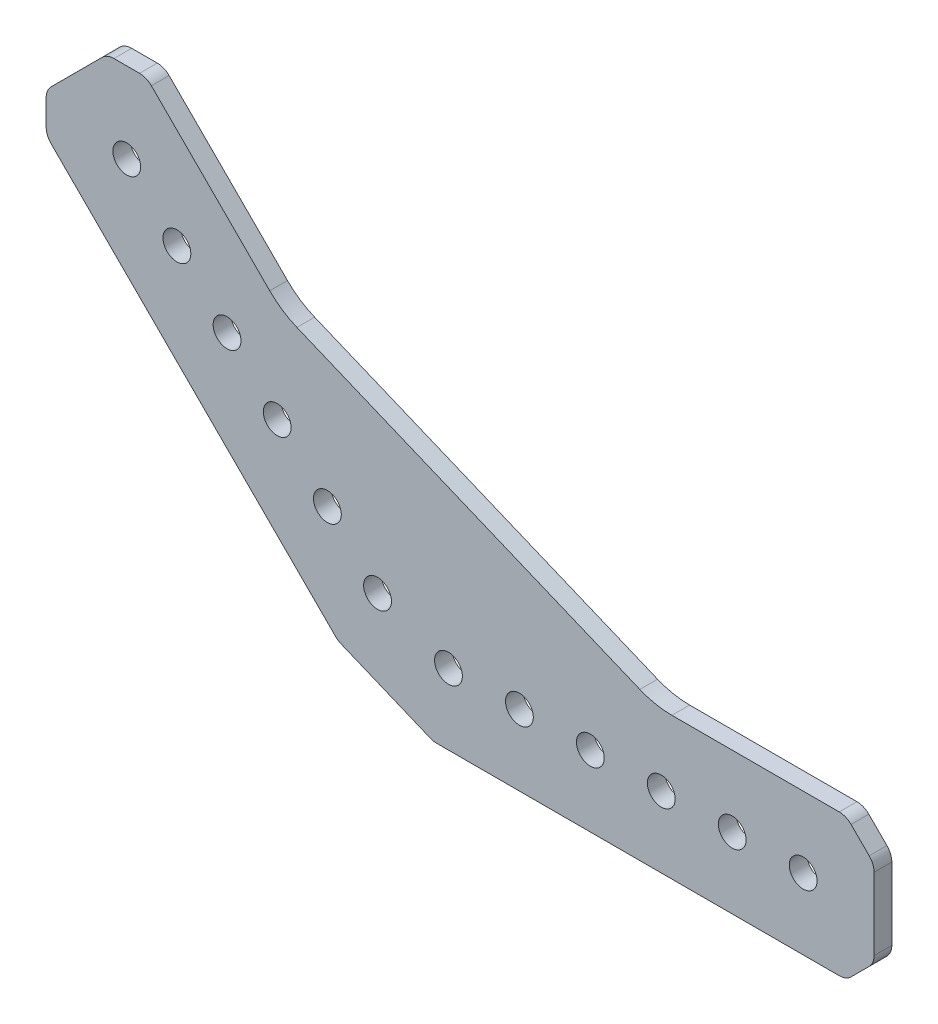
SolidWorks part; units mm, degrees
material "5052-H32"
ref_plane "Front Plane" through (0, 0, 0) normal (0, 0, 1) x (1, 0, 0)
ref_plane "Top Plane" through (0, 0, 0) normal (0, 1, 0) x (1, 0, 0)
ref_plane "Right Plane" through (0, 0, 0) normal (1, 0, 0) x (0, 0, -1)
ref_plane "Plane1" through (0, 0, 3.175) normal (0, 0, 1) x (1, 0, 0)
sketch "Sketch1" plane through (0, 0, 3.175) normal (0, 0, 1) x (1, 0, 0)
  line L0 (-6.5198, 6.8427) -> (9.4487, 0.2284)
  line L1 (10.5967, 0) -> (82.6574, 0)
  line L2 (84.7787, 0.8787) -> (88.0213, 4.1213)
  line L3 (88.9, 6.2426) -> (88.9, 19.1574)
  line L4 (88.0213, 21.2787) -> (84.7787, 24.5213)
  line L5 (82.6574, 25.4) -> (52.7016, 25.4)
  line L6 (46.9613, 26.5418) -> (-14.4388, 51.9746)
  line L7 (-19.3051, 55.2262) -> (-40.4871, 76.4081)
  line L8 (-42.6084, 77.2868) -> (-47.1942, 77.2868)
  line L9 (-49.3155, 76.4081) -> (-58.4476, 67.276)
  line L10 (-59.3263, 65.1547) -> (-59.3263, 60.5689)
  line L11 (-58.4476, 58.4476) -> (-7.493, 7.493)
  circle A0 centre (0, 17.9605) radius 2.4892
  circle A1 centre (12.7, 12.7) radius 2.4892
  circle A2 centre (63.5, 12.7) radius 2.4892
  circle A3 centre (38.1, 12.7) radius 2.4892
  circle A4 centre (-17.9605, 35.921) radius 2.4892
  circle A5 centre (-35.921, 53.8815) radius 2.4892
  circle A6 centre (76.2, 12.7) radius 2.4892
  circle A7 centre (50.8, 12.7) radius 2.4892
  circle A8 centre (25.4, 12.7) radius 2.4892
  circle A9 centre (-8.9803, 26.9408) radius 2.4892
  circle A10 centre (-26.9408, 44.9013) radius 2.4892
  circle A11 centre (-44.9013, 62.8618) radius 2.4892
  arc A12 (9.4487, 0.2284) -> (10.5967, 0) centre (10.5967, 3) ccw
  arc A13 (82.6574, 0) -> (84.7787, 0.8787) centre (82.6574, 3) ccw
  arc A14 (88.0213, 4.1213) -> (88.9, 6.2426) centre (85.9, 6.2426) ccw
  arc A15 (88.9, 19.1574) -> (88.0213, 21.2787) centre (85.9, 19.1574) ccw
  arc A16 (84.7787, 24.5213) -> (82.6574, 25.4) centre (82.6574, 22.4) ccw
  arc A17 (52.7016, 25.4) -> (46.9613, 26.5418) centre (52.7016, 40.4) cw
  arc A18 (-14.4388, 51.9746) -> (-19.3051, 55.2262) centre (-8.6985, 65.8328) cw
  arc A19 (-40.4871, 76.4081) -> (-42.6084, 77.2868) centre (-42.6084, 74.2868) ccw
  arc A20 (-47.1942, 77.2868) -> (-49.3155, 76.4081) centre (-47.1942, 74.2868) ccw
  arc A21 (-58.4476, 67.276) -> (-59.3263, 65.1547) centre (-56.3263, 65.1547) ccw
  arc A22 (-59.3263, 60.5689) -> (-58.4476, 58.4476) centre (-56.3263, 60.5689) ccw
  arc A23 (-7.493, 7.493) -> (-6.5198, 6.8427) centre (-5.3717, 9.6143) ccw
extrude "Boss-Extrude1" add sketch "Sketch1" against normal blind 3.175
